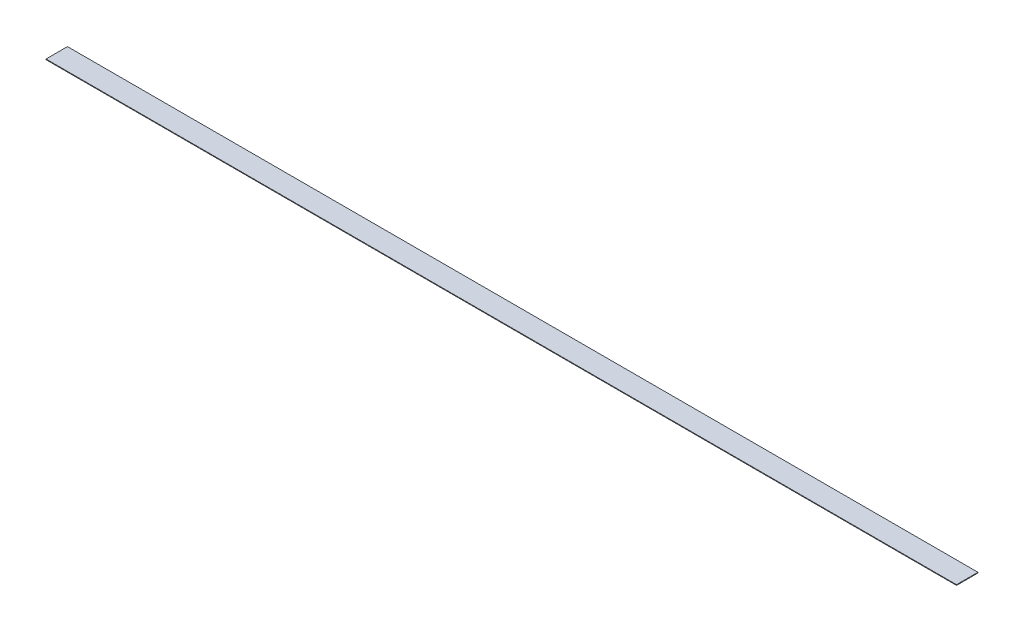
SolidWorks part; units mm, degrees
ref_plane "Front Plane" through (0, 0, 0) normal (0, 0, 1) x (1, 0, 0)
ref_plane "Top Plane" through (0, 0, 0) normal (0, 1, 0) x (1, 0, 0)
ref_plane "Right Plane" through (0, 0, 0) normal (1, 0, 0) x (0, 0, -1)
sketch "Sketch1" plane through (0, 0, 0) normal (0, 1, 0) x (1, 0, 0)
  line L1 (336.55, 7.9375) -> (-336.55, 7.9375)
  line L2 (336.55, 7.9375) -> (336.55, -7.9375)
  line L3 (336.55, -7.9375) -> (-336.55, -7.9375)
  line L4 (-336.55, 7.9375) -> (-336.55, -7.9375)
  line L5 (336.55, 7.9375) -> (-336.55, -7.9375) construction
  line L6 (336.55, -7.9375) -> (-336.55, 7.9375) construction
  point P0 (0, 0)
  dimension "D1" = 673.1
  dimension "D2" = 15.875
extrude "Boss-Extrude1" add sketch "Sketch1" along normal blind 0.4572
